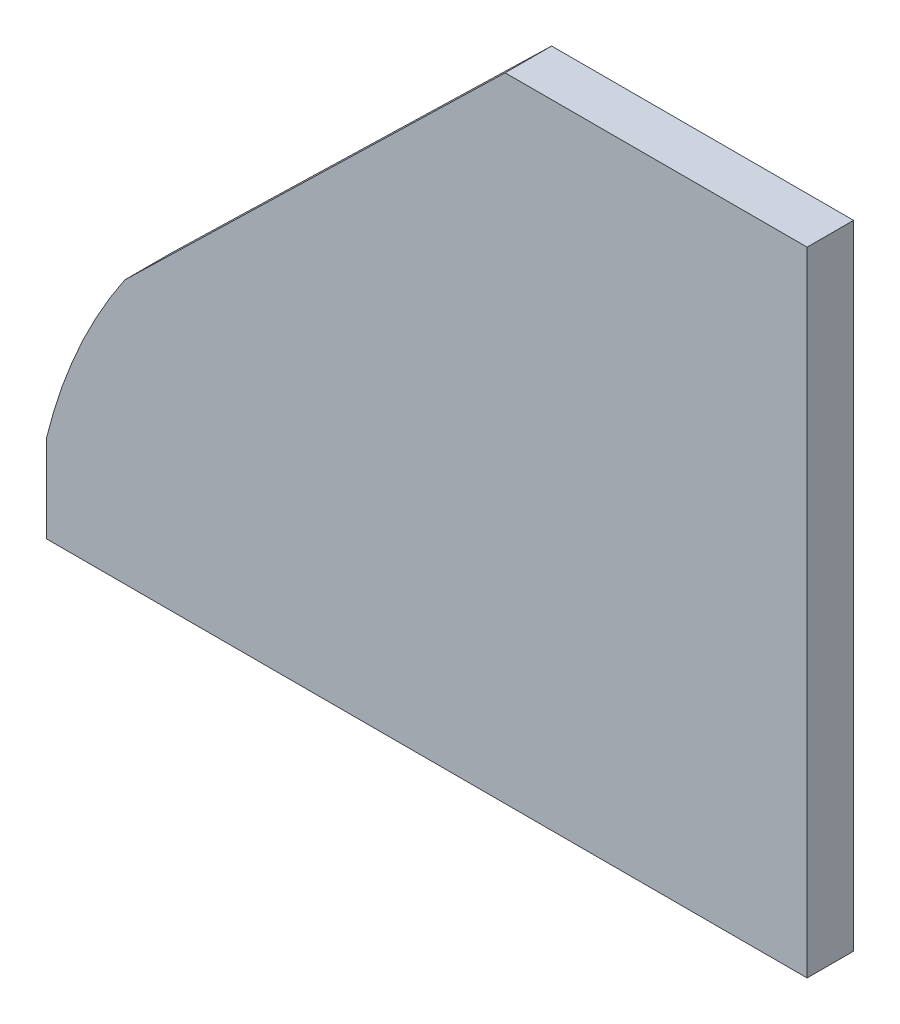
SolidWorks part; units mm, degrees
ref_plane "Ön Düzlem" through (0, 0, 0) normal (0, 0, 1) x (1, 0, 0)
ref_plane "Üst Düzlem" through (0, 0, 0) normal (0, 1, 0) x (1, 0, 0)
ref_plane "Sağ Düzlem" through (0, 0, 0) normal (1, 0, 0) x (0, 0, -1)
sketch "Çizim1" plane through (0, 0, 0) normal (0, 0, 1) x (1, 0, 0)
  line L0 (0, 0) -> (131, 0)
  line L1 (131, 0) -> (131, 109)
  line L2 (131, 109) -> (79, 109)
  line L3 (0, 0) -> (0, 15)
  line L4 (724.958, -506.7525) -> (742.1286, -15.0523) construction
  line L5 (12.9638, 44.8572) -> (79, 109)
  arc A0 (0, 15) -> (13.5106, 45.3884) centre (90.3336, -6.9646) cw
  dimension "D1" = 131
  dimension "D2" = 109
  dimension "D3" = 52
  dimension "D4" = 15
extrude "Yükseklik-Ekstrüzyon1" add sketch "Çizim1" along normal blind 8 contours A0 L3 L0 L1 L2 L5
